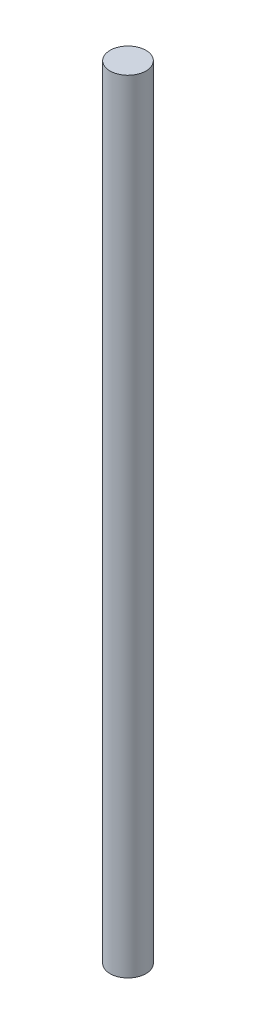
SolidWorks part; units mm, degrees
ref_plane "Front Plane" through (0, 0, 0) normal (0, 0, 1) x (1, 0, 0)
ref_plane "Top Plane" through (0, 0, 0) normal (0, 1, 0) x (1, 0, 0)
ref_plane "Right Plane" through (0, 0, 0) normal (1, 0, 0) x (0, 0, -1)
sketch "Sketch1" plane through (0, 0, 0) normal (0, 1, 0) x (1, 0, 0)
  circle A0 centre (0, 0) radius 2.5
  dimension "D1" = 5
extrude "Boss-Extrude1" add sketch "Sketch1" along normal blind 109
sketch "Sketch2" plane through (0, 0, 0) normal (0, -1, 0) x (1, 0, 0)
  line L0 (-2.0576, 1.42) -> (2.0576, 1.42)
  line L1 (-2.5, 0) -> (2.5, 0) construction
  line L2 (-2.0576, -1.42) -> (2.0576, -1.42)
  circle A0 centre (0, 0) radius 2.5 construction
  arc A1 (-2.0576, -1.42) -> (2.0576, -1.42) centre (0, 0) ccw
  arc A2 (2.0576, 1.42) -> (-2.0576, 1.42) centre (0, 0) ccw
  point P9 (0, 0)
  dimension "D1" = 1.42
